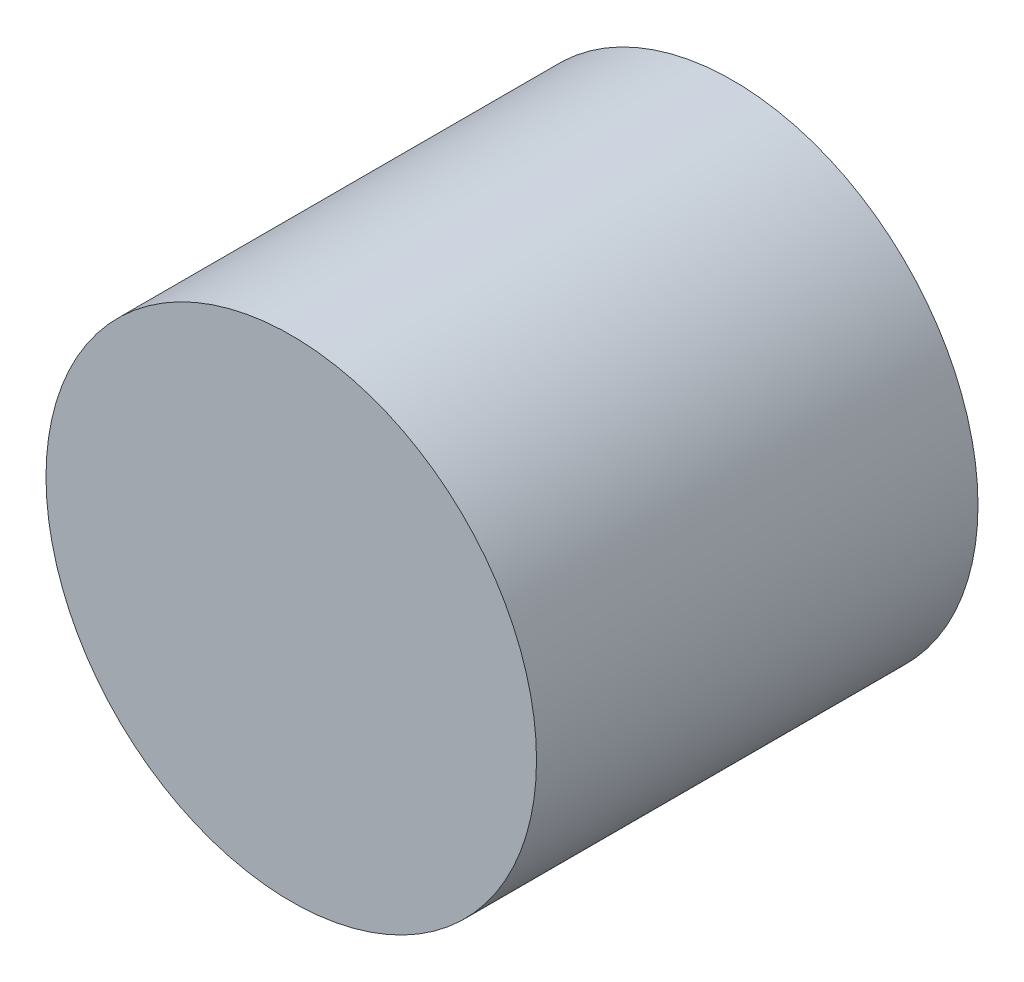
SolidWorks part; units mm, degrees
ref_plane "Alzado" through (0, 0, 0) normal (0, 0, 1) x (1, 0, 0)
ref_plane "Planta" through (0, 0, 0) normal (0, 1, 0) x (1, 0, 0)
ref_plane "Vista lateral" through (0, 0, 0) normal (1, 0, 0) x (0, 0, -1)
sketch "Croquis1" plane through (0, 0, 0) normal (0, 0, 1) x (1, 0, 0)
  circle A0 centre (0, 0) radius 1
  dimension "D1" = 2
extrude "Saliente-Extruir1" add sketch "Croquis1" along normal blind 1.8
